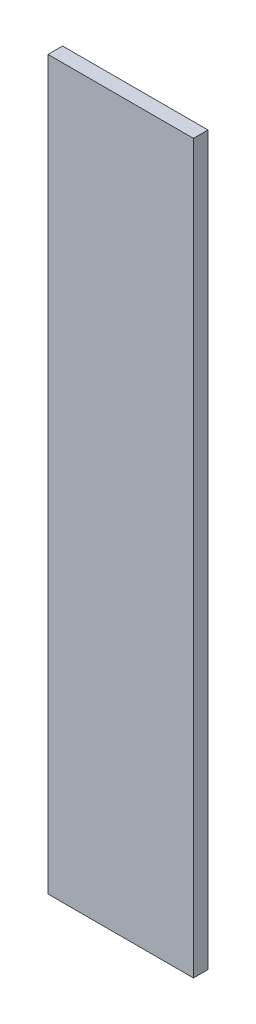
SolidWorks part; units mm, degrees
ref_plane "Front Plane" through (0, 0, 0) normal (0, 0, 1) x (1, 0, 0)
ref_plane "Top Plane" through (0, 0, 0) normal (0, 1, 0) x (1, 0, 0)
ref_plane "Right Plane" through (0, 0, 0) normal (1, 0, 0) x (0, 0, -1)
sketch "Sketch1" plane through (0, 0, 0) normal (0, 0, 1) x (1, 0, 0)
  line L1 (-5, -25) -> (5, -25)
  line L2 (-5, -25) -> (-5, 25)
  line L3 (-5, 25) -> (5, 25)
  line L4 (5, -25) -> (5, 25)
  line L5 (-5, -25) -> (5, 25) construction
  line L6 (-5, 25) -> (5, -25) construction
  point P0 (0, 0)
  dimension "D1" = 50
  dimension "D2" = 10
extrude "Boss-Extrude1" add sketch "Sketch1" along normal blind 1
